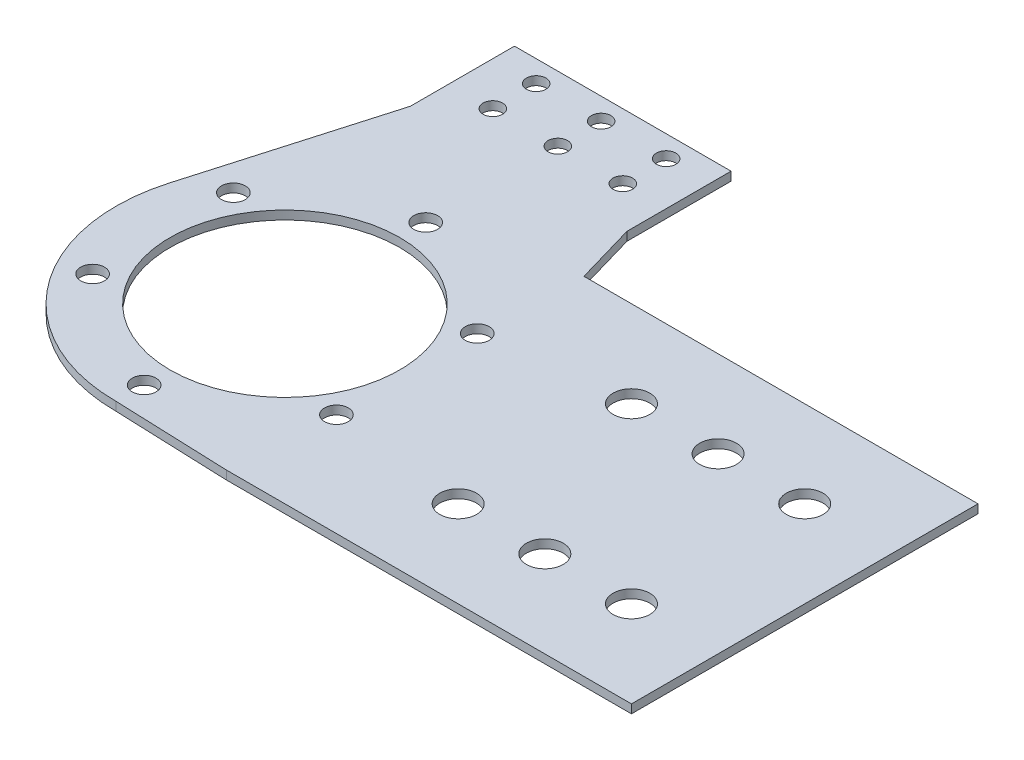
SolidWorks part; units mm, degrees
ref_plane "Front Plane" through (0, 0, 0) normal (0, 0, 1) x (1, 0, 0)
ref_plane "Top Plane" through (0, 0, 0) normal (0, 1, 0) x (1, 0, 0)
ref_plane "Right Plane" through (0, 0, 0) normal (1, 0, 0) x (0, 0, -1)
sketch "Sketch1" plane through (0, 0, 0) normal (0, 1, 0) x (1, 0, 0)
  circle A0 centre (0, 0) radius 45 construction
  circle A1 centre (0, 0) radius 39
  circle A2 centre (0, 0) radius 26.5
  circle A3 centre (0, 0) radius 32.5 construction
  dimension "D1" = 90
  dimension "D2" = 65
  dimension "D3" = 78
  dimension "D4" = 53
extrude "Boss-Extrude1" add sketch "Sketch1" along normal mid plane 2
sketch "Sketch3" plane through (0, 0, 0) normal (0, 1, 0) x (1, 0, 0)
  line L0 (0, 0) -> (0, 78) construction
  line L2 (-25, 78) -> (25, 78)
  line L3 (-25, 78) -> (-25, 26.5)
  line L4 (-25, 26.5) -> (25, 26.5)
  line L5 (25, 78) -> (25, 26.5)
  line L6 (0, 26.5) -> (0, 78) construction
  line L7 (-25, 52.25) -> (25, 52.25) construction
  circle A0 centre (0, 0) radius 26.5 construction
  point P3 (0, 52.25)
  dimension "D1" = 78
  dimension "D2" = 50
extrude "Boss-Extrude2" add sketch "Sketch3" along normal mid plane 2
sketch "Sketch4" plane through (0, 0, 0) normal (0, 1, 0) x (1, 0, 0)
  line L0 (-25, 53.9666) -> (-37.4668, 10.8276)
  line L1 (-25, 78) -> (-25, 29.9333) construction
  line L2 (-37.4668, 10.8276) -> (-25, 29.9333)
  line L3 (-25, 29.9333) -> (-25, 53.9666)
  line L4 (0, 0) -> (0, 78) construction
  line L5 (25, 78) -> (-25, 78) construction
  line L6 (37.4668, 10.8276) -> (25, 29.9333)
  line L7 (25, 53.9666) -> (37.4668, 10.8276)
  line L8 (25, 29.9333) -> (25, 53.9666)
  arc A0 (-25, 29.9333) -> (25, 29.9333) centre (0, 0) ccw construction
extrude "Boss-Extrude3" add sketch "Sketch4" along normal mid plane 2
sketch "Sketch7" plane through (0, 0, 0) normal (0, 1, 0) x (1, 0, 0)
  line L0 (0, 0) -> (73.25, 0) construction
  line L1 (120, -40) -> (26.5, -40)
  line L2 (120, -40) -> (120, 40)
  line L4 (120, 40) -> (26.5, 40)
  line L5 (26.5, 0) -> (120, 0) construction
  line L6 (73.25, -40) -> (73.25, 40) construction
  line L13 (26.5, -40) -> (0, -39)
  line L14 (0, -39) -> (26.5, -15.7283)
  line L15 (26.5, -15.7283) -> (26.5, 0)
  line L16 (26.5, 0) -> (26.5, 40)
  circle A1 centre (0, 0) radius 26.5 construction
  arc A3 (-37.4668, 10.8276) -> (37.4668, 10.8276) centre (0, 0) ccw construction
  dimension "D1" = 80
  dimension "D2" = 120
extrude "Boss-Extrude5" add sketch "Sketch7" along normal mid plane 2
sketch "Sketch2" plane through (0, 0, 0) normal (0, 1, 0) x (1, 0, 0)
  circle A0 centre (0, 0) radius 32.5 construction
  circle A1 centre (0, 32.5) radius 2.75
  dimension "D1" = 65
  dimension "D2" = 5.5
extrude "Cut-Extrude1" cut sketch "Sketch2" against normal through all both and the other way through all contours A1
pattern_circular "CirPattern1" count 6 over 360 about axis through (0, 0, 0) along (0, 1, 0) of "Cut-Extrude1"
sketch "Sketch5" plane through (0, 1, 0) normal (0, 1, 0) x (1, 0, 0)
  line L0 (-25, 73) -> (25, 73) construction
  line L1 (-25, 78) -> (-25, 53.9666) construction
  line L2 (25, 53.9666) -> (25, 78) construction
  line L3 (25, 78) -> (-25, 78) construction
  circle A0 centre (0, 73) radius 2.25
  dimension "D1" = 4.5
  dimension "D2" = 5
extrude "Cut-Extrude2" cut sketch "Sketch5" against normal through all both and the other way through all
pattern_linear "LPattern1" count 2 spacing 15 along (1, 0, 0) count 2 spacing 10 along (0, 0, 1) of "Cut-Extrude2"
pattern_linear "LPattern2" count 2 spacing 15 along (-1, 0, 0) count 2 spacing 10 along (0, 0, 1) of "Cut-Extrude2"
sketch "Sketch8" plane through (0, 1, 0) normal (0, 1, 0) x (1, 0, 0)
  line L0 (120, 0) -> (0, 0) construction
  line L1 (120, -40) -> (120, 40) construction
  line L3 (60, -20) -> (71.5056, -20) construction
  line L4 (60, -20) -> (60, 20) construction
  line L5 (60, 20) -> (71.5056, 20) construction
  line L6 (71.5056, -20) -> (71.5056, 20) construction
  line L7 (65.7528, 20) -> (65.7528, -20) construction
  line L8 (60, 0) -> (71.5056, 0) construction
  circle A0 centre (60, 20) radius 4.25
  circle A1 centre (60, -20) radius 4.25
  point P5 (65.7528, 0)
  dimension "D1" = 8.5
  dimension "D2" = 40
  dimension "D3" = 60
extrude "Cut-Extrude3" cut sketch "Sketch8" against normal through all both and the other way through all
pattern_linear "LPattern3" count 3 spacing 20 along (1, 0, 0) of "Cut-Extrude3"
